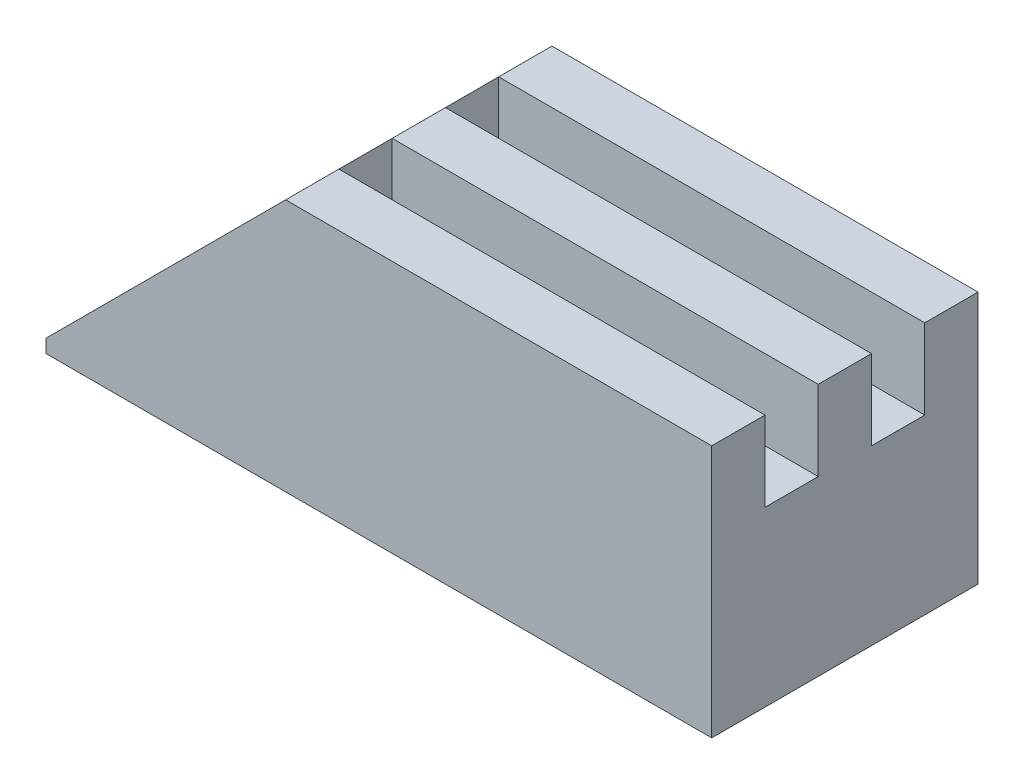
SolidWorks part; units mm, degrees
ref_plane "Front Plane" through (0, 0, 0) normal (0, 0, 1) x (1, 0, 0)
ref_plane "Top Plane" through (0, 0, 0) normal (0, 1, 0) x (1, 0, 0)
ref_plane "Right Plane" through (0, 0, 0) normal (1, 0, 0) x (0, 0, -1)
sketch "Sketch1" plane through (0, 0, 0) normal (0, 1, 0) x (1, 0, 0)
  line L1 (-12.5, -5) -> (12.5, -5)
  line L2 (-12.5, -5) -> (-12.5, 5)
  line L3 (-12.5, 5) -> (12.5, 5)
  line L4 (12.5, -5) -> (12.5, 5)
  line L5 (-12.5, -5) -> (12.5, 5) construction
  line L6 (-12.5, 5) -> (12.5, -5) construction
  point P0 (0, 0)
  dimension "D1" = 10
  dimension "D2" = 25
extrude "Boss-Extrude1" add sketch "Sketch1" along normal blind 9.5
chamfer "Chamfer1" distance 9 angle 45 1 edges at (-12.5, 9.5, 0)
sketch "Sketch3" plane through (0, 9.5, 0) normal (0, 1, 0) x (1, 0, 0)
  line L0 (12.5, 0) -> (-3.5, 0) construction
  line L2 (-3.5, -1) -> (12.5, -1)
  line L3 (-3.5, -1) -> (-3.5, 1)
  line L4 (12.5, 5) -> (-3.5, 5)
  line L5 (-3.5, 5) -> (-3.5, -5)
  line L6 (-3.5, -5) -> (12.5, -5)
  line L7 (12.5, -5) -> (12.5, 5)
  line L8 (12.5, 5) -> (-3.5, 5)
  line L9 (-3.5, 5) -> (-3.5, -5)
  line L10 (-3.5, -5) -> (12.5, -5)
  line L11 (12.5, -5) -> (12.5, 5)
  line L12 (-3.5, 1) -> (12.5, 1)
  line L13 (12.5, -1) -> (12.5, 1)
  line L14 (-3.5, -1) -> (12.5, 1) construction
  line L15 (-3.5, 1) -> (12.5, -1) construction
  line L16 (12.5, 5) -> (-3.5, 5)
  line L17 (12.5, 5) -> (12.5, 3)
  line L18 (12.5, 3) -> (-3.5, 3)
  line L19 (-3.5, 5) -> (-3.5, 3)
  line L20 (12.5, -5) -> (-3.5, -5)
  line L21 (12.5, -5) -> (12.5, -3)
  line L22 (12.5, -3) -> (-3.5, -3)
  line L23 (-3.5, -5) -> (-3.5, -3)
  point P6 (4.5, 0)
  line M14 (-3.5, 5) -> (-3.5, -5)
  dimension "D2" = 2
  dimension "D3" = 2
  dimension "D4" = 2
  dimension "D1" = 0
extrude "Cut-Extrude2" cut sketch "Sketch3" against normal blind 3 contours L11 L18 L9 L12 | L22 L11 L2 M14
sketch "Sketch4" plane through (-6.5, 6.5, 0) normal (-0.7071, 0.7071, 0) x (0, 0, 1)
  line L0 (0, 0) -> (0, 4.2426) construction
  line L8 (-5, 4.2426) -> (-5, -8.4853)
  line L9 (-5, -8.4853) -> (5, -8.4853)
  line L10 (5, -8.4853) -> (5, 4.2426)
  line L11 (5, 4.2426) -> (3, 4.2426)
  line L12 (3, 4.2426) -> (1, 4.2426)
  line L13 (1, 4.2426) -> (-1, 4.2426)
  line L14 (-1, 4.2426) -> (-3, 4.2426)
  line L15 (-3, 4.2426) -> (-5, 4.2426)
  line L16 (-5, 4.2426) -> (-5, -8.4853)
  line L17 (-5, -8.4853) -> (5, -8.4853)
  line L18 (5, -8.4853) -> (5, 4.2426)
  line L19 (5, 4.2426) -> (3, 4.2426)
  line L20 (3, 4.2426) -> (1, 4.2426)
  line L21 (1, 4.2426) -> (-1, 4.2426)
  line L22 (-1, 4.2426) -> (-3, 4.2426)
  line L23 (-3, 4.2426) -> (-5, 4.2426)
  circle A0 centre (0, 1.3926) radius 1.25
  dimension "D2" = 2.85
  dimension "D3" = 2.5
  dimension "D1" = 0
extrude "Cut-Extrude3" cut sketch "Sketch4" against normal blind 4 contours A0
